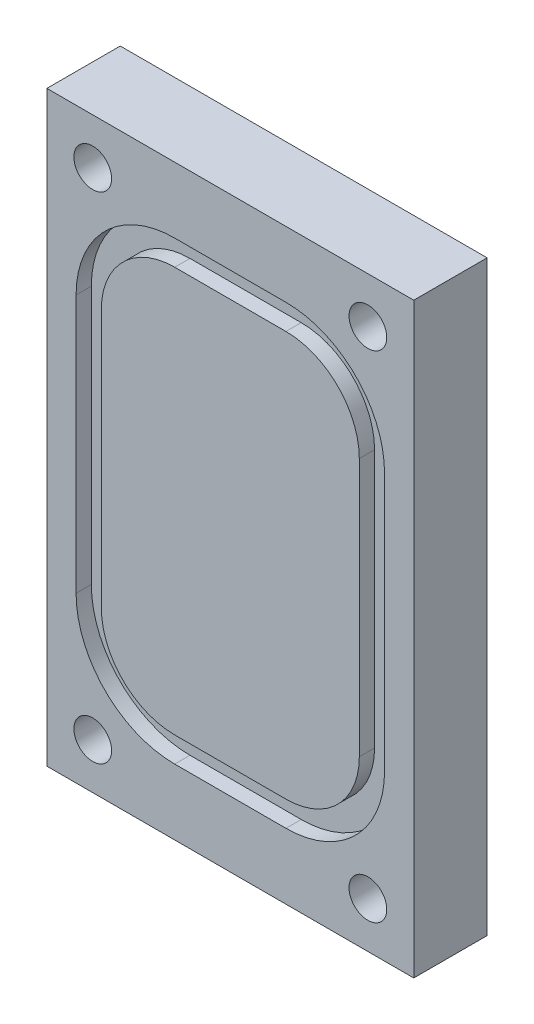
SolidWorks part; units mm, degrees
material "6061 Alloy"
ref_plane "Front Plane" through (0, 0, 0) normal (0, 0, 1) x (1, 0, 0)
ref_plane "Top Plane" through (0, 0, 0) normal (0, 1, 0) x (1, 0, 0)
ref_plane "Right Plane" through (0, 0, 0) normal (1, 0, 0) x (0, 0, -1)
sketch "Sketch1" plane through (0, 0, 0) normal (0, 0, 1) x (1, 0, 0)
  line L1 (-15.875, -25.4) -> (15.875, -25.4)
  line L2 (-15.875, -25.4) -> (-15.875, 25.4)
  line L3 (-15.875, 25.4) -> (15.875, 25.4)
  line L4 (15.875, -25.4) -> (15.875, 25.4)
  line L5 (-15.875, -25.4) -> (15.875, 25.4) construction
  line L6 (-15.875, 25.4) -> (15.875, -25.4) construction
  point P0 (0, 0)
  dimension "D1" = 31.75
  dimension "D2" = 50.8
extrude "Boss-Extrude1" add sketch "Sketch1" along normal blind 6.35
sketch "Sketch3" plane through (0, 0, 6.35) normal (0, 0, 1) x (1, 0, 0)
  line L0 (13.3477, -11.176) -> (13.3477, 11.176)
  line L1 (-4.8133, -17.526) -> (4.8133, -17.526)
  line L2 (-11.1633, -11.176) -> (-11.1633, 11.176)
  line L3 (-4.8133, 17.526) -> (4.8133, 17.526)
  line L4 (11.1633, -11.176) -> (11.1633, 11.176)
  line L5 (-11.1633, -17.526) -> (11.1633, 17.526) construction
  line L6 (-11.1633, 17.526) -> (11.1633, -17.526) construction
  line L7 (-4.8133, -19.7104) -> (4.8133, -19.7104)
  line L8 (-13.3477, -11.176) -> (-13.3477, 11.176)
  line L9 (-4.8133, 19.7104) -> (4.8133, 19.7104)
  arc A0 (-4.8133, -17.526) -> (-11.1633, -11.176) centre (-4.8133, -11.176) cw
  arc A1 (4.8133, -17.526) -> (11.1633, -11.176) centre (4.8133, -11.176) ccw
  arc A2 (4.8133, 17.526) -> (11.1633, 11.176) centre (4.8133, 11.176) cw
  arc A3 (-11.1633, 11.176) -> (-4.8133, 17.526) centre (-4.8133, 11.176) cw
  arc A4 (4.8133, 19.7104) -> (13.3477, 11.176) centre (4.8133, 11.176) cw
  arc A5 (4.8133, -19.7104) -> (13.3477, -11.176) centre (4.8133, -11.176) ccw
  arc A6 (-4.8133, -19.7104) -> (-13.3477, -11.176) centre (-4.8133, -11.176) cw
  arc A7 (-13.3477, 11.176) -> (-4.8133, 19.7104) centre (-4.8133, 11.176) cw
  point P0 (0, 0)
  dimension "D1" = 6.35
  dimension "D2" = 9.6266
  dimension "D3" = 22.352
  dimension "D4" = 2.1844
extrude "Cut-Extrude2 - dash 027" cut sketch "Sketch3" against normal blind 1.3208
hole_wizard "CSK for #4 Flat Head Machine Screw (100)1" positions "Sketch7" profile "Sketch6" countersink size "#4" standard "Ansi Inch" end condition through all
sketch "Sketch7" plane through (0, 0, 0) normal (0, 0, -1) x (-1, 0, 0)
  line L0 (-15.875, 25.4) -> (15.875, 25.4) construction
  line L1 (15.875, -25.4) -> (-15.875, -25.4) construction
  point P0 (-11.9062, 21.4312)
  point P1 (11.9062, 21.4312)
  point P3 (-11.9062, -21.4313)
  point P5 (11.9062, -21.4313)
  dimension "D1" = 3.9688
  dimension "D2" = 3.9688
  dimension "D3" = 11.9062
  dimension "D4" = 11.9062
sketch "Sketch6" plane through (11.9062, 21.4312, 0) normal (1, 0, 0) x (0, 1, 0)
  line L0 (0, 0) -> (0, 6.35)
  line L1 (0, 6.35) -> (1.6319, 6.35)
  line L2 (1.6319, 6.35) -> (1.6319, 1.0284)
  line L3 (1.6319, 1.0284) -> (2.8575, 0)
  line L5 (2.8575, 0) -> (0, 0)
  line L6 (-1.6319, 1.0284) -> (-2.8575, 0) construction
  line L11 (0, -6.35) -> (0, 107.95) construction
  dimension "Thru Hole Dia." = 3.2639
  dimension "Thru Hole Depth" = 6.35
  dimension "Near C'Sink Dia." = 5.715
  dimension "Near C'Sink Angle" = 100
